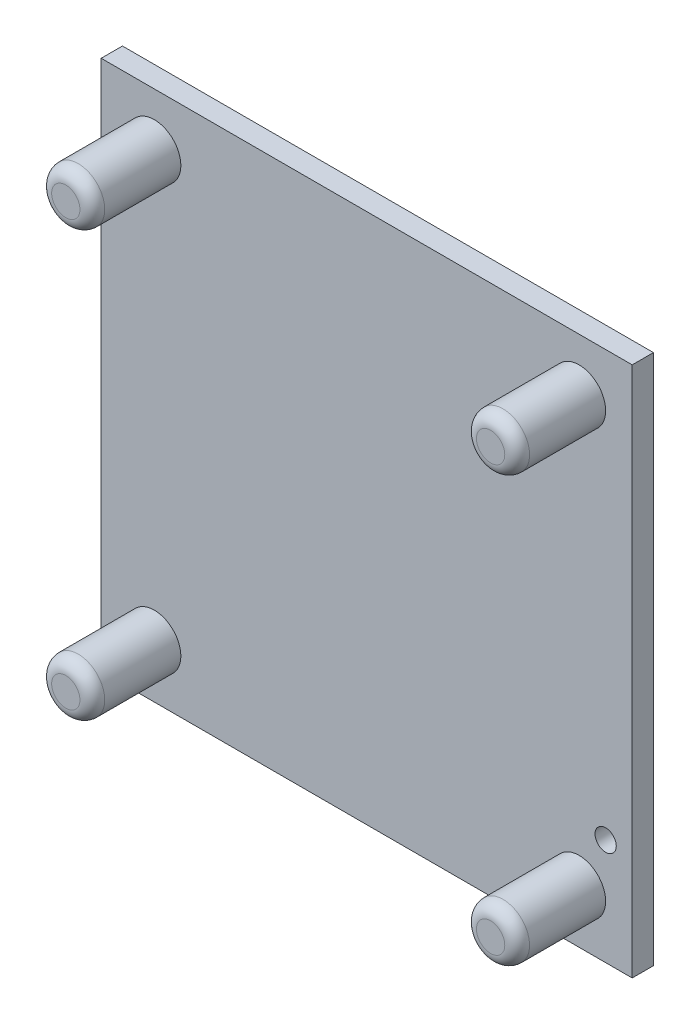
SolidWorks part; units mm, degrees
material "1060 Alloy"
ref_plane "Front Plane" through (0, 0, 0) normal (0, 0, 1) x (1, 0, 0)
ref_plane "Top Plane" through (0, 0, 0) normal (0, 1, 0) x (1, 0, 0)
ref_plane "Right Plane" through (0, 0, 0) normal (1, 0, 0) x (0, 0, -1)
sketch "Sketch2" plane through (0, 0, 0) normal (0, 0, 1) x (1, 0, 0)
  line L1 (-150, 150) -> (150, 150)
  line L2 (-150, 150) -> (-150, -150)
  line L3 (-150, -150) -> (150, -150)
  line L4 (150, 150) -> (150, -150)
  line L5 (-150, 150) -> (150, -150) construction
  line L6 (-150, -150) -> (150, 150) construction
  point P0 (0, 0)
  dimension "D1" = 300
  dimension "D2" = 300
extrude "Boss-Extrude1" add sketch "Sketch2" along normal blind 12
sketch "Sketch3" plane through (0, 0, 12) normal (0, 0, 1) x (1, 0, 0)
  line L0 (-150, -150) -> (150, -150) construction
  line L1 (-150, 150) -> (-150, -150) construction
  circle A0 centre (120, -120) radius 15
  circle A1 centre (-120, -120) radius 15
  circle A2 centre (-120, 120) radius 15
  circle A3 centre (120, 120) radius 15
  dimension "D1" = 30
  dimension "D3" = 30
  dimension "D2" = 30
  dimension "D4" = 2
  dimension "D5" = 2
extrude "Boss-Extrude2" add sketch "Sketch3" along normal blind 50
fillet "Fillet1" radius 7 4 edges at (-105, -120, 62) (135, -120, 62) (135, 120, 62) (-105, 120, 62)
hole_wizard "Ø12.0 (12) Diameter Hole1" positions "Sketch5" profile "Sketch6" hole size "Ø12.0" standard "Ansi Metric" end condition through all
sketch "Sketch5" plane through (0, 0, 12) normal (0, 0, 1) x (1, 0, 0)
  line L0 (150, -150) -> (150, 150) construction
  line L3 (-150, -150) -> (150, -150) construction
  point P0 (135, -90)
  dimension "D1" = 15
  dimension "D2" = 60
sketch "Sketch6" plane through (135, -90, 12) normal (1, 0, 0) x (0, -1, 0)
  line L0 (0, 0) -> (0, 12)
  line L1 (0, 12) -> (6, 12)
  line L2 (6, 12) -> (6, 0)
  line L5 (6, 0) -> (0, 0)
  line L11 (0, -6.35) -> (0, 107.95) construction
  dimension "Thru Hole Dia." = 12
  dimension "Thru Hole Depth" = 12
